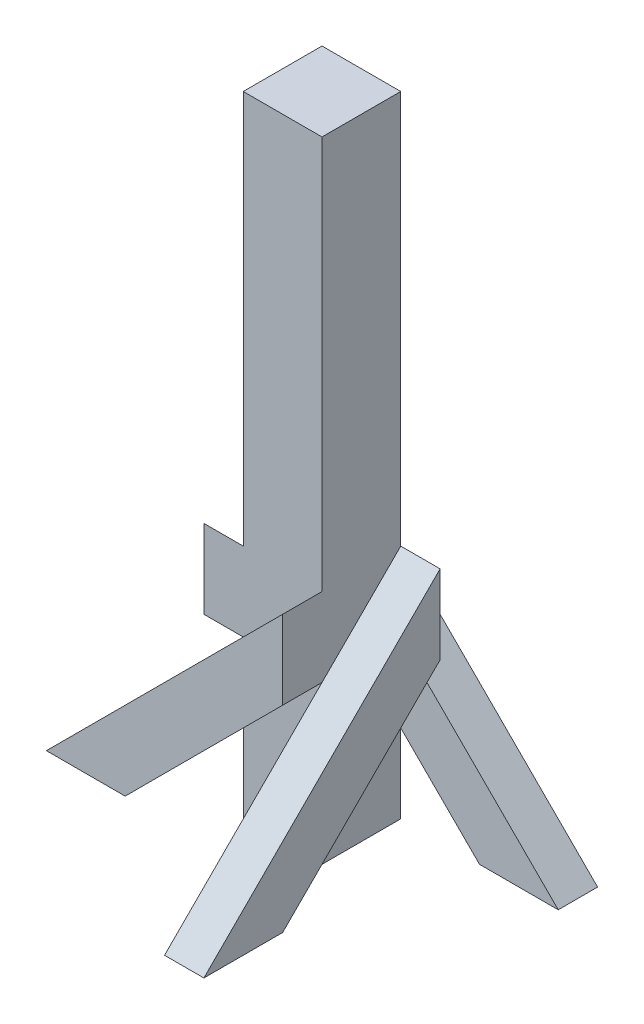
SolidWorks part; units mm, degrees
material "Pine"
ref_plane "Front Plane" through (0, 0, 0) normal (0, 0, 1) x (1, 0, 0)
ref_plane "Top Plane" through (0, 0, 0) normal (0, 1, 0) x (1, 0, 0)
ref_plane "Right Plane" through (0, 0, 0) normal (1, 0, 0) x (0, 0, -1)
sketch "Sketch1" plane through (0, 0, 0) normal (0, 1, 0) x (1, 0, 0)
  line L1 (-57.912, 61.976) -> (43.688, 61.976)
  line L2 (-57.912, 61.976) -> (-57.912, -39.624)
  line L3 (-57.912, -39.624) -> (43.688, -39.624)
  line L4 (43.688, 61.976) -> (43.688, -39.624)
  dimension "D1" = 101.6
  dimension "D2" = 101.6
extrude "Boss-Extrude1" add sketch "Sketch1" along normal blind 812.8 contours L1 L4 L3 L2
sketch "Sketch2" plane through (-57.912, 0, 0) normal (-1, 0, 0) x (0, 0, 1)
  line L1 (-163.576, 0) -> (39.624, 203.2)
  line L2 (-265.176, 0) -> (39.624, 304.8)
  line L4 (39.624, 812.8) -> (39.624, 0) construction
  line L5 (-265.176, 0) -> (-163.576, 0)
  line L6 (39.624, 304.8) -> (39.624, 203.2)
  line L7 (-61.976, 0) -> (39.624, 0) construction
  line L8 (-265.176, 0) -> (39.624, 0) construction
  dimension "D1" = 101.6
  dimension "D2" = 101.6
  dimension "D3" = 45
  dimension "D4" = 45
  dimension "D5" = 304.8
sketch "Sketch3" plane through (0, 0, -61.976) normal (0, 0, -1) x (-1, 0, 0)
  line L1 (-145.288, 0) -> (57.912, 203.2)
  line L2 (-246.888, 0) -> (57.912, 304.8)
  line L5 (-246.888, 0) -> (-145.288, 0)
  line L6 (57.912, 304.8) -> (57.912, 203.2)
  line L8 (-246.888, 0) -> (57.912, 0) construction
  line L9 (57.912, 812.8) -> (57.912, 0) construction
  line L10 (57.912, 0) -> (-43.688, 0) construction
  dimension "D1" = 101.6
  dimension "D2" = 101.6
  dimension "D3" = 45
  dimension "D4" = 45
  dimension "D5" = 304.8
sketch "Sketch5" plane through (0, 0, 39.624) normal (0, 0, 1) x (1, 0, 0)
  line L1 (-159.512, 0) -> (43.688, 203.2)
  line L2 (-261.112, 0) -> (43.688, 304.8)
  line L4 (43.688, 812.8) -> (43.688, 0) construction
  line L5 (-261.112, 0) -> (-159.512, 0)
  line L6 (43.688, 304.8) -> (43.688, 203.2)
  line L7 (-57.912, 0) -> (43.688, 0) construction
  line L8 (-261.112, 0) -> (43.688, 0) construction
  dimension "D1" = 101.6
  dimension "D2" = 101.6
  dimension "D3" = 45
  dimension "D4" = 45
  dimension "D5" = 304.8
extrude "Boss-Extrude2" add sketch "Sketch2" along normal blind 50.8
extrude "Boss-Extrude3" add sketch "Sketch3" along normal blind 50.8
extrude "Boss-Extrude4" add sketch "Sketch5" along normal blind 50.8
sketch "Sketch7" plane through (43.688, 0, 0) normal (1, 0, 0) x (0, 0, -1)
  line L1 (-141.224, 0) -> (61.976, 203.2)
  line L2 (-242.824, 0) -> (61.976, 304.8)
  line L5 (-242.824, 0) -> (-141.224, 0)
  line L6 (61.976, 304.8) -> (61.976, 203.2)
  line L8 (-242.824, 0) -> (61.976, 0) construction
  line L9 (61.976, 812.8) -> (61.976, 203.2) construction
  line L10 (61.976, 0) -> (-39.624, 0) construction
  dimension "D1" = 101.6
  dimension "D2" = 101.6
  dimension "D3" = 45
  dimension "D4" = 45
  dimension "D5" = 304.8
extrude "Boss-Extrude6" add sketch "Sketch7" along normal blind 50.8
